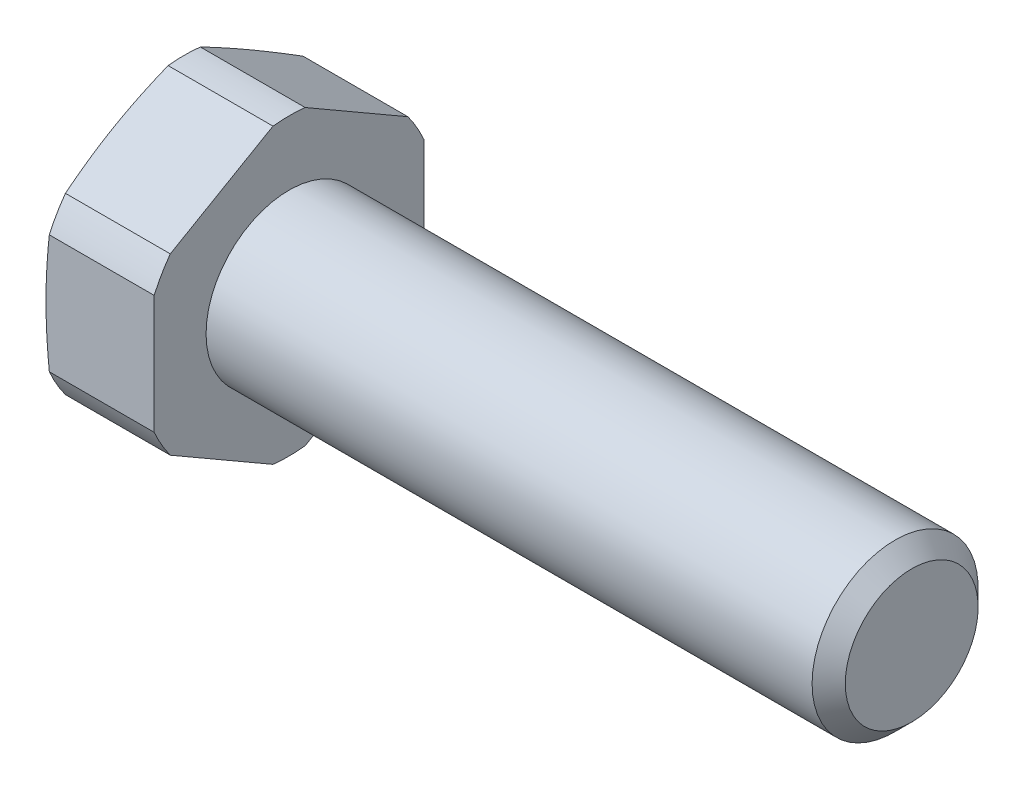
SolidWorks part; units mm, degrees
material "AISI 1020"
ref_plane "Спереди" through (0, 0, 0) normal (0, 0, 1) x (1, 0, 0)
ref_plane "Сверху" through (0, 0, 0) normal (0, 1, 0) x (1, 0, 0)
ref_plane "Справа" through (0, 0, 0) normal (1, 0, 0) x (0, 0, -1)
sketch "Эскиз1" plane through (0, 0, 0) normal (0, 0, 1) x (1, 0, 0)
  line L0 (-1000, 0) -> (49000, 0) construction
  line L1 (-5.3, 0) -> (-5.3, 6.175)
  line L2 (-5.3, 6.175) -> (-5.0521, 7.1)
  line L3 (-5.0521, 7.1) -> (0, 7.1)
  line L4 (0, 7.1) -> (0, 4)
  line L5 (0, 4) -> (29.2, 4)
  line L6 (30, 3.2) -> (30, 0)
  line L7 (30, 4) -> (30.625, 5.0825) construction
  line L8 (30.625, 5.0825) -> (31.25, 4) construction
  line L9 (31.25, 4) -> (30, 4) construction
  line L10 (30.625, 5.0825) -> (30.625, 4) construction
  line L11 (30.625, 5.0825) -> (8.625, 5.0825) construction
  line L12 (29.2, 4) -> (30, 3.2)
  line L13 (30, 4) -> (29.6, 3.6) construction
  line L14 (-5.3, 6.175) -> (-18.3, 6.175) construction
  line L15 (-5.3, 0) -> (30, 0)
  dimension "l_" = 30
  dimension "D2" = 15
revolve "Повернуть1" add sketch "Эскиз1" angle 360 about L0
cosmetic thread "Условное изображение резьбы1" parameters "D1"=22, "D2"=5.8349
sketch "Эскиз2" plane through (-5.3, 0, 0) normal (-1, 0, 0) x (0, 0, 1)
  line L1 (0, 7.5056) -> (-6.5, 3.7528)
  line L2 (-6.5, 3.7528) -> (-6.5, -3.7528)
  line L3 (-6.5, -3.7528) -> (0, -7.5056)
  line L4 (0, -7.5056) -> (6.5, -3.7528)
  line L5 (6.5, -3.7528) -> (6.5, 3.7528)
  line L6 (6.5, 3.7528) -> (0, 7.5056)
  circle A0 centre (0, 0) radius 6.5 construction
extrude "Вырез-Вытянуть1" cut sketch "Эскиз2" against normal up to surface (35.3 mm away) flip side to cut up to face at (30, 0, 3.2)
equation "\"D1@Эскиз1\"=\"_d_@Эскиз1\"/10"
equation "\"D@Эскиз1\"=\"S_@Эскиз1\"*0.95"
equation "\"D1@Эскиз2\"=\"S_@Эскиз1\""
equation "\"D1@Условное изображение резьбы1\"=\"b_@Эскиз1\""
equation "\"D2@Условное изображение резьбы1\"=\"_d_@Эскиз1\"-\"dr@Эскиз1\"*2"
